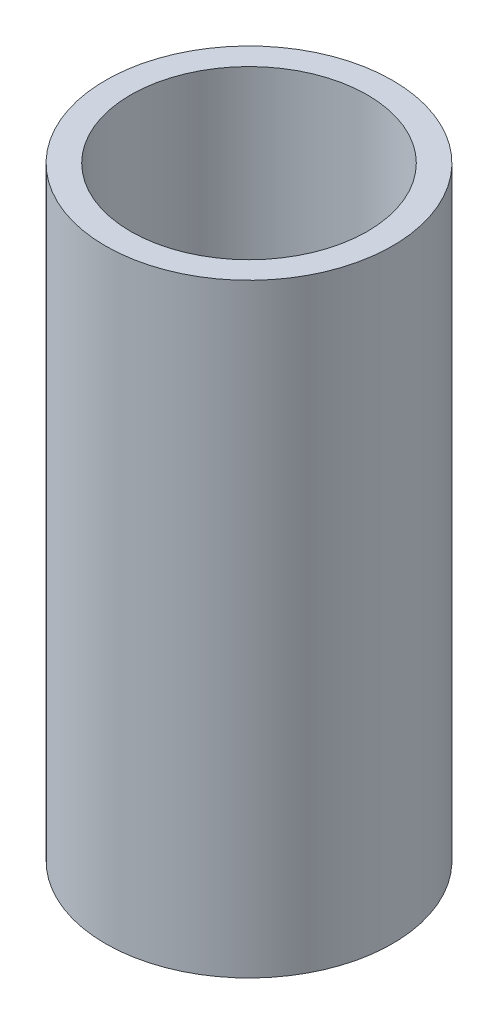
SolidWorks part; units mm, degrees
ref_plane "Plan de face" through (0, 0, 0) normal (0, 0, 1) x (1, 0, 0)
ref_plane "Plan de dessus" through (0, 0, 0) normal (0, 1, 0) x (1, 0, 0)
ref_plane "Plan de droite" through (0, 0, 0) normal (1, 0, 0) x (0, 0, -1)
sketch "Esquisse1" plane through (0, 0, 0) normal (0, 1, 0) x (1, 0, 0)
  circle A0 centre (0, 0) radius 2.35
  circle A1 centre (0, 0) radius 2.85
  dimension "D1" = 5.7
  dimension "D2" = 0.5
extrude "Boss.-Extru.1" add sketch "Esquisse1" along normal blind 12
